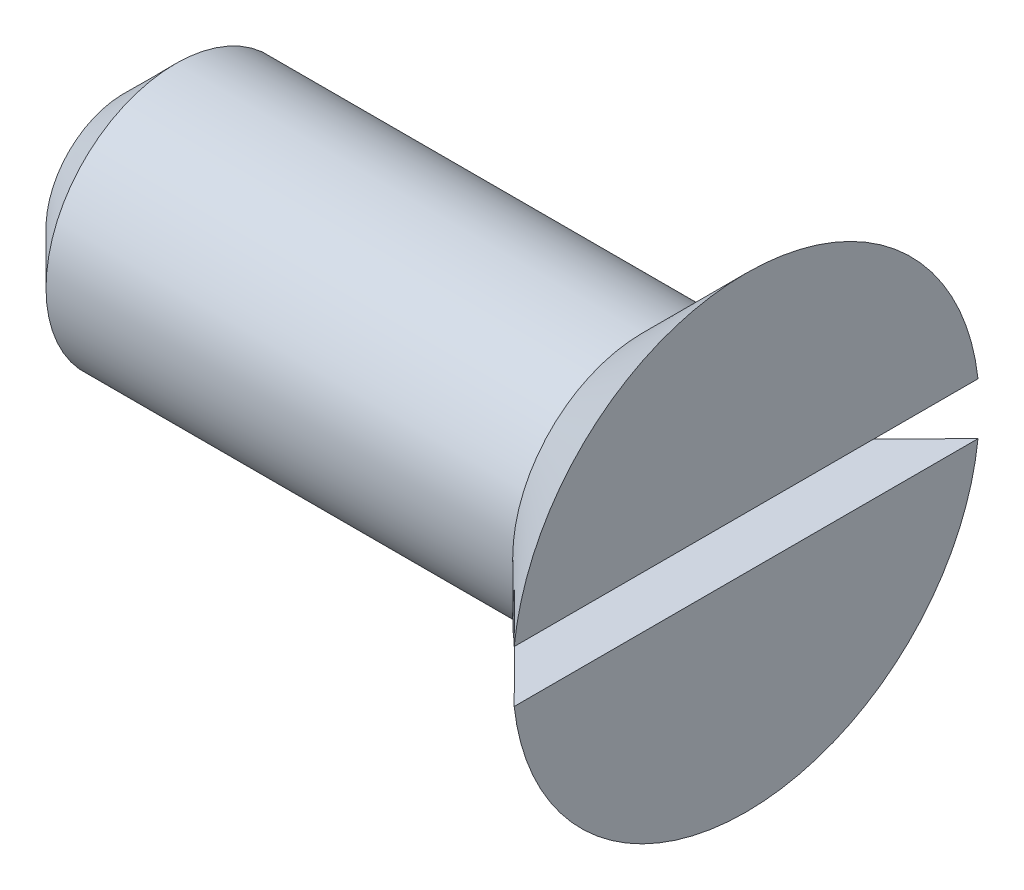
SolidWorks part; units mm, degrees
ref_plane "Спереди" through (0, 0, 0) normal (0, 0, 1) x (1, 0, 0)
ref_plane "Сверху" through (0, 0, 0) normal (0, 1, 0) x (1, 0, 0)
ref_plane "Справа" through (0, 0, 0) normal (1, 0, 0) x (0, 0, -1)
sketch "Эскиз1" plane through (0, 0, 0) normal (0, 1, 0) x (1, 0, 0)
  line L0 (0, 0) -> (12, 0)
  line L5 (0, 2.5) -> (0, 0)
  line L6 (0, 2.5) -> (10, 2.5)
  line L7 (10, 2.5) -> (12, 4.5)
  line L8 (12, 4.5) -> (12, 0)
  dimension "D1" = 2.5
  dimension "D2" = 2
  dimension "D3" = 12
  dimension "D4" = 45
revolve "Повернуть1" add sketch "Эскиз1" angle 360 about L0
chamfer "Фаска1" distance 1 angle 45 1 edges at (0, 0, 2.5)
sketch "Эскиз2" plane through (12, 0, 0) normal (1, 0, 0) x (0, 0, -1)
  line L1 (4.8288, -0.5) -> (-4.8288, -0.5)
  line L2 (4.8288, -0.5) -> (4.8288, 0.5)
  line L3 (4.8288, 0.5) -> (-4.8288, 0.5)
  line L4 (-4.8288, -0.5) -> (-4.8288, 0.5)
  line L5 (4.8288, -0.5) -> (-4.8288, 0.5) construction
  line L6 (4.8288, 0.5) -> (-4.8288, -0.5) construction
  point P0 (0, 0)
  dimension "D1" = 1
extrude "Вырез-Вытянуть1" cut sketch "Эскиз2" against normal blind 1
